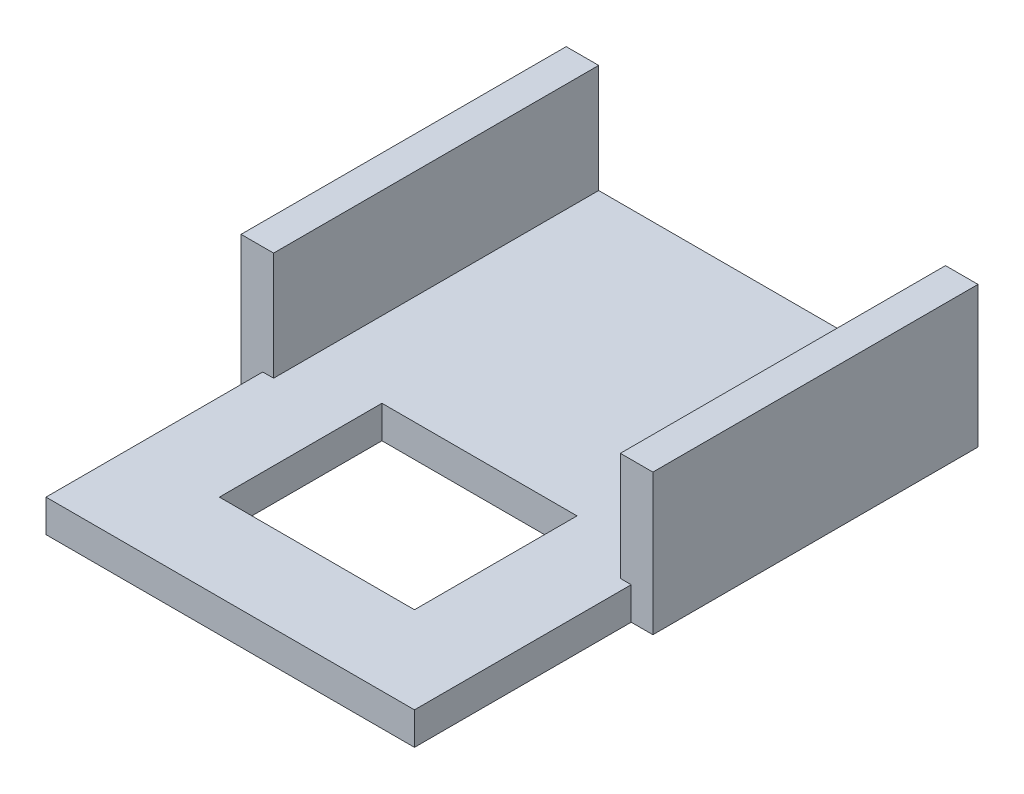
SolidWorks part; units mm, degrees
ref_plane "Front" through (0, 0, 0) normal (0, 0, 1) x (1, 0, 0)
ref_plane "Top" through (0, 0, 0) normal (0, 1, 0) x (1, 0, 0)
ref_plane "Right" through (0, 0, 0) normal (1, 0, 0) x (0, 0, -1)
sketch "Sketch1" plane through (0, 0, 0) normal (0, 0, 1) x (1, 0, 0)
  line L0 (-1.9, 0.65) -> (-1.6, 0.65)
  line L1 (1.9, 0.65) -> (1.9, -0.65)
  line L2 (1.9, -0.65) -> (-1.9, -0.65)
  line L3 (-1.9, -0.65) -> (-1.9, 0.65)
  line L4 (-1.6, 0.65) -> (-1.6, -0.35)
  line L5 (1.9, 0.65) -> (1.6, 0.65)
  line L6 (1.6, 0.65) -> (1.6, -0.35)
  line L7 (1.6, -0.35) -> (-1.6, -0.35)
extrude "Основание" add sketch "Sketch1" along normal blind 3
sketch "Sketch8" plane through (0, 0, 3) normal (0, 0, 1) x (1, 0, 0)
  line L0 (-1.7, -0.65) -> (1.7, -0.65)
  line L1 (-1.9, -0.65) -> (1.9, -0.65) construction
  line L2 (1.7, -0.35) -> (-1.7, -0.35)
  line L3 (1.6, -0.35) -> (-1.6, -0.35) construction
  line L4 (-1.7, -0.35) -> (-1.7, -0.65)
  line L5 (1.7, -0.35) -> (1.7, -0.65)
extrude "Верхушка" add sketch "Sketch8" along normal blind 2
sketch "Sketch9" plane through (0, -0.65, 0) normal (0, -1, 0) x (1, 0, 0)
  line L6 (-0.9, 4.2) -> (-0.9, 2.7)
  line L7 (-0.9, 4.2) -> (0.9, 4.2)
  line L8 (0.9, 4.2) -> (0.9, 2.7)
  line L9 (0.9, 2.7) -> (-0.9, 2.7)
extrude "прорезь" cut sketch "Sketch9" against normal blind 2
